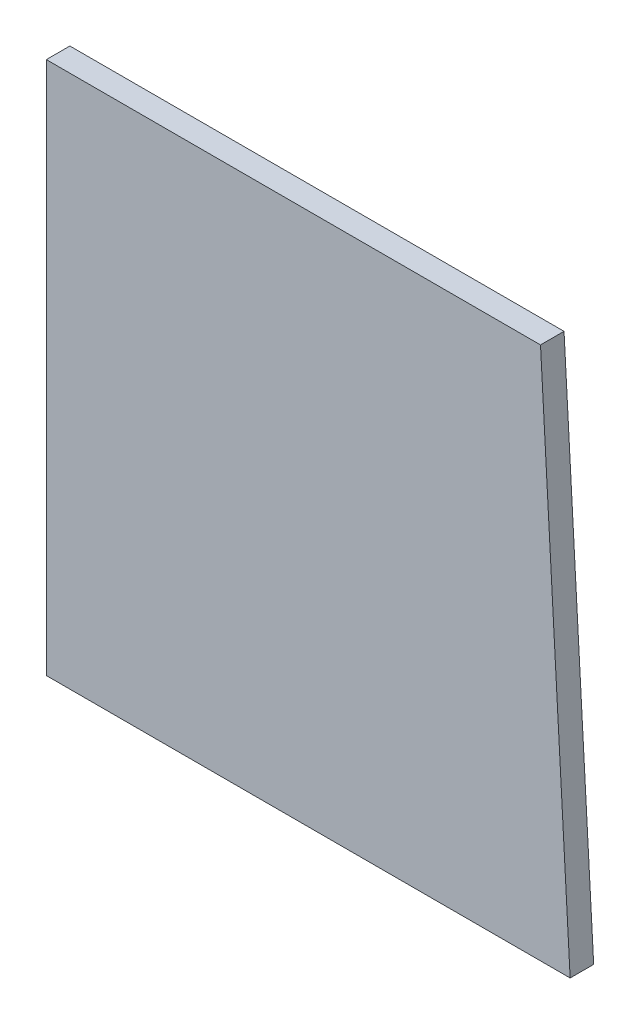
SolidWorks part; units mm, degrees
ref_plane "Front Plane" through (0, 0, 0) normal (0, 0, 1) x (1, 0, 0)
ref_plane "Top Plane" through (0, 0, 0) normal (0, 1, 0) x (1, 0, 0)
ref_plane "Right Plane" through (0, 0, 0) normal (1, 0, 0) x (0, 0, -1)
sketch "Sketch1" plane through (0, 0, 0) normal (0, 0, 1) x (1, 0, 0)
  line L0 (-33.5908, -33.18) -> (33.1808, -33.18)
  line L1 (29.403, 34.82) -> (33.1808, -33.18)
  line L2 (-33.5908, 34.82) -> (-33.5908, -33.18)
  line L3 (29.403, 34.82) -> (-33.5908, 34.82)
  dimension "D1" = 62.9938
  dimension "D2" = 68
extrude "Boss-Extrude1" add sketch "Sketch1" along normal blind 3
